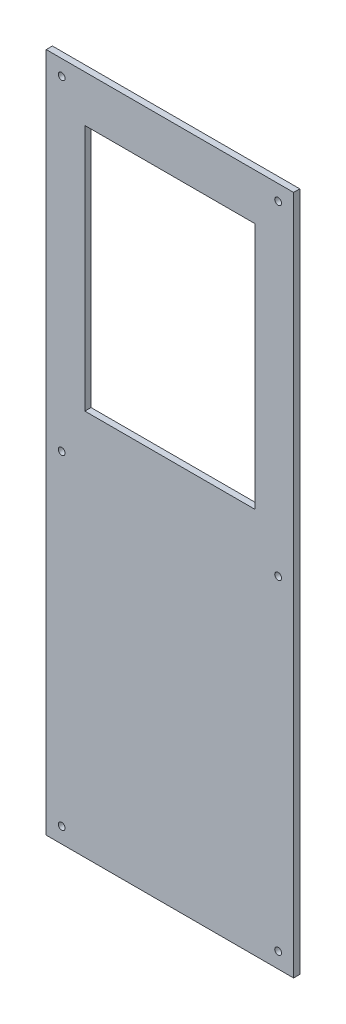
SolidWorks part; units mm, degrees
ref_plane "Plan de face" through (0, 0, 0) normal (0, 0, 1) x (1, 0, 0)
ref_plane "Plan de dessus" through (0, 0, 0) normal (0, 1, 0) x (1, 0, 0)
ref_plane "Plan de droite" through (0, 0, 0) normal (1, 0, 0) x (0, 0, -1)
sketch "Esquisse1" plane through (0, 0, 0) normal (0, 0, 1) x (1, 0, 0)
  line L0 (0, 220) -> (0, 0) construction
  line L1 (80, 220) -> (-80, 220)
  line L2 (80, 220) -> (80, -220)
  line L3 (80, -220) -> (-80, -220)
  line L4 (-80, 220) -> (-80, -220)
  line L5 (80, 220) -> (-80, -220) construction
  line L6 (80, -220) -> (-80, 220) construction
  line L7 (0, 0) -> (80, 0) construction
  line L8 (-70, 220) -> (-70, -220) construction
  line L9 (-70, -220) -> (-80, -210) construction
  line L10 (-80, -210) -> (80, -210) construction
  line L11 (-80, 210) -> (80, 210) construction
  line L12 (70, 220) -> (70, -220) construction
  line L14 (-55, 190) -> (55, 190)
  line L15 (-55, 190) -> (-55, 30)
  line L16 (-55, 30) -> (55, 30)
  line L17 (55, 190) -> (55, 30)
  line L18 (-55, 190) -> (55, 30) construction
  line L19 (-55, 30) -> (55, 190) construction
  circle A0 centre (70, 0) radius 2.2
  circle A1 centre (70, 210) radius 2.2
  circle A2 centre (70, -210) radius 2.2
  circle A3 centre (-70, 210) radius 2.2
  circle A4 centre (-70, 0) radius 2.2
  circle A5 centre (-70, -210) radius 2.2
  point P0 (0, 0)
  point P29 (0, 110)
  dimension "D5" = 4.4
  dimension "D6" = 4.4
  dimension "D7" = 4.4
  dimension "D1" = 160
  dimension "D2" = 440
  dimension "D3" = 10
  dimension "D4" = 10
  dimension "D8" = 110
  dimension "D9" = 160
  dimension "D10" = 20
extrude "Boss.-Extru.1" add sketch "Esquisse1" along normal blind 4
